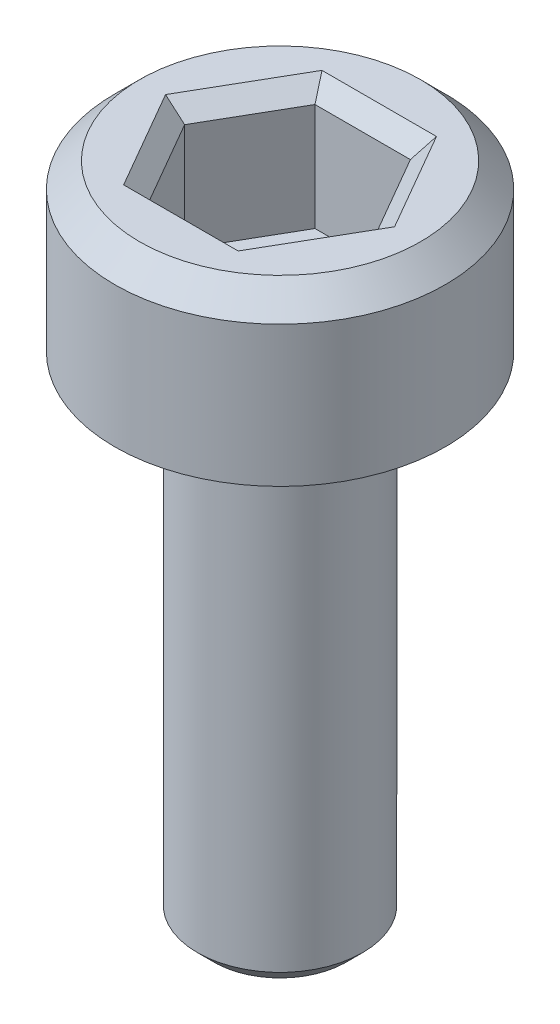
SolidWorks part; units mm, degrees
ref_plane "Front Plane" through (0, 0, 0) normal (0, 0, 1) x (1, 0, 0)
ref_plane "Top Plane" through (0, 0, 0) normal (0, 1, 0) x (1, 0, 0)
ref_plane "Right Plane" through (0, 0, 0) normal (1, 0, 0) x (0, 0, -1)
sketch "Sketch1" plane through (0, 0, 0) normal (0, 1, 0) x (1, 0, 0)
  circle A0 centre (0, 0) radius 2
  dimension "D1" = 4
extrude "Boss-Extrude1" add sketch "Sketch1" along normal blind 2
chamfer "Chamfer1" distance 0.3 angle 45 1 edges at (0, 2, 2)
sketch "Sketch2" plane through (0, 2, 0) normal (0, 1, 0) x (1, 0, 0)
  line L1 (1.1547, 0) -> (0.5774, 1)
  line L2 (0.5774, 1) -> (-0.5774, 1)
  line L3 (-0.5774, 1) -> (-1.1547, 0)
  line L4 (-1.1547, 0) -> (-0.5774, -1)
  line L5 (-0.5774, -1) -> (0.5774, -1)
  line L6 (0.5774, -1) -> (1.1547, 0)
  circle A0 centre (0, 0) radius 1 construction
  dimension "D1" = 2
extrude "Cut-Extrude1" cut sketch "Sketch2" against normal blind 1.5
chamfer "Chamfer2" distance 0.2 angle 45 6 edges at (0.866, 2, -0.5) (0.866, 2, 0.5) (0, 2, 1) (-0.866, 2, 0.5) (-0.866, 2, -0.5) (0, 2, -1)
sketch "Sketch3" plane through (0, 0, 0) normal (0, -1, 0) x (1, 0, 0)
  circle A0 centre (0, 0) radius 1
  dimension "D1" = 2
extrude "Boss-Extrude2" add sketch "Sketch3" along normal blind 6
chamfer "Chamfer3" distance 0.2 angle 45 1 edges at (0, -6, -1)
